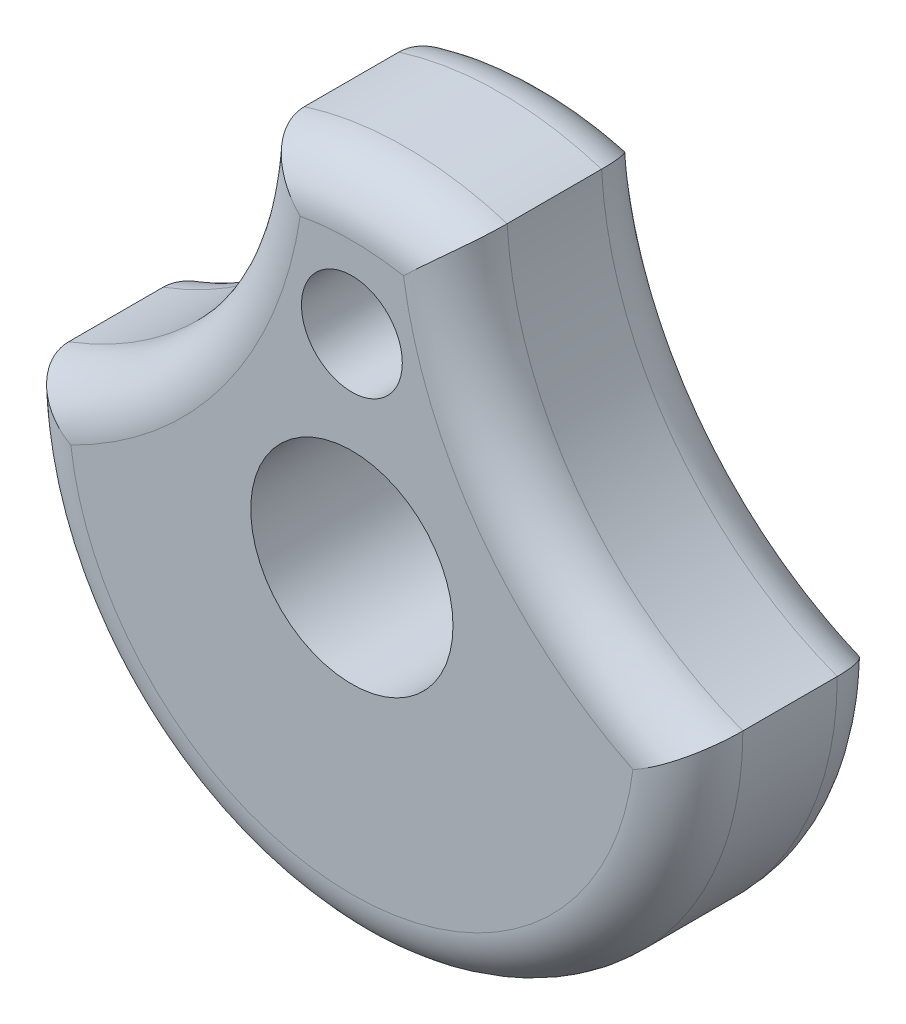
SolidWorks part; units mm, degrees
material "Plain Carbon Steel"
ref_plane "Front Plane" through (0, 0, 0) normal (0, 0, 1) x (1, 0, 0)
ref_plane "Top Plane" through (0, 0, 0) normal (0, 1, 0) x (1, 0, 0)
ref_plane "Right Plane" through (0, 0, 0) normal (1, 0, 0) x (0, 0, -1)
sketch "Sketch1" plane through (0, 0, 0) normal (0, 0, 1) x (1, 0, 0)
  circle A0 centre (0, 0) radius 15.875
  circle A1 centre (0, 0) radius 4.7625
  circle A2 centre (0, 9.525) radius 2.3749
  dimension "D1" = 31.75
  dimension "D2" = 9.525
  dimension "D3" = 4.7498
  dimension "D4" = 9.525
extrude "Boss-Extrude1" add sketch "Sketch1" against normal blind 9.525
sketch "Sketch2" plane through (0, 0, 0) normal (0, 0, 1) x (1, 0, 0)
  line L0 (0, 0) -> (0, -15.875) construction
  arc A0 (-15.875, 0) -> (-4.7752, 15.1398) centre (-21.8959, 16.053) ccw
  circle A1 centre (0, 0) radius 15.875 construction
  arc A2 (15.875, 0) -> (4.7752, 15.1398) centre (21.8959, 16.053) cw
  arc A3 (15.875, 0) -> (4.7752, 15.1398) centre (0, 0) ccw
  arc A4 (-4.7752, 15.1398) -> (-15.875, 0) centre (0, 0) ccw
  dimension "D1" = 17.145
  dimension "D2" = 4.7752
  dimension "D3" = 9.5504
  dimension "D4" = 4.7752
extrude "Cut-Extrude1" cut sketch "Sketch2" against normal through all
fillet "Fillet1" radius 2.54 4 edges at (8.0689, 5.9157, 0) (0, -15.875, 0) (0, 15.875, 0) (-8.0689, 5.9157, 0)
fillet "Fillet2" radius 2.54 4 edges at (8.0689, 5.9157, -9.525) (0, -15.875, -9.525) (0, 15.875, -9.525) (-8.0689, 5.9157, -9.525)
